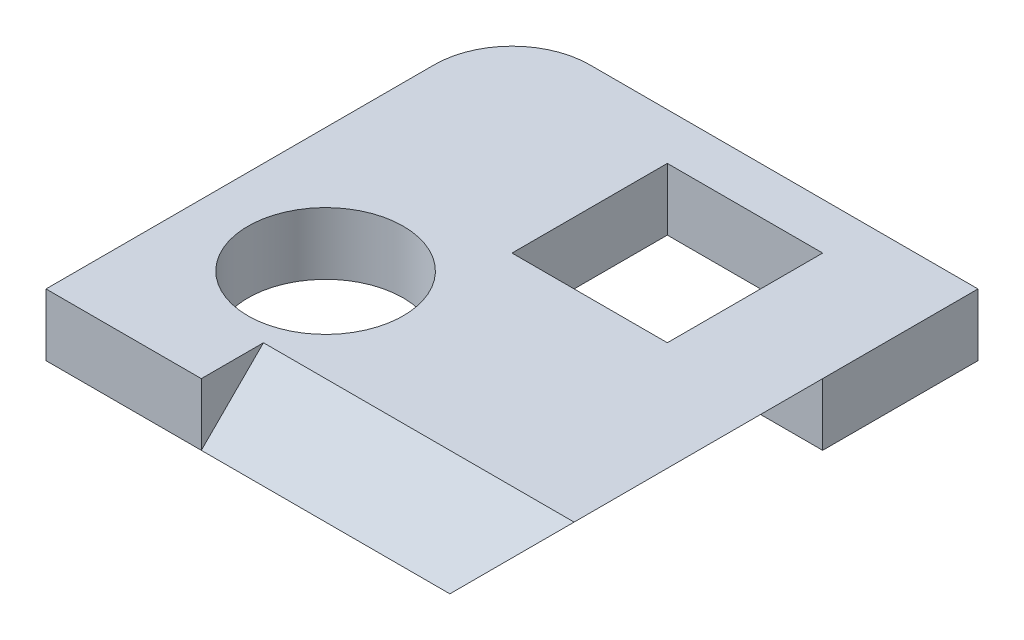
SolidWorks part; units mm, degrees
ref_plane "Ebene vorne" through (0, 0, 0) normal (0, 0, 1) x (1, 0, 0)
ref_plane "Ebene oben" through (0, 0, 0) normal (0, 1, 0) x (1, 0, 0)
ref_plane "Ebene rechts" through (0, 0, 0) normal (1, 0, 0) x (0, 0, -1)
sketch "Sketch1" plane through (0, 0, 0) normal (0, 1, 0) x (1, 0, 0)
  line L1 (0, 0) -> (30, 0)
  line L2 (0, 0) -> (0, 30)
  line L3 (0, 30) -> (30, 30)
  line L4 (30, 0) -> (30, 30)
  dimension "D1" = 30
extrude "Boss-Extrude1" add sketch "Sketch1" along normal blind 4
sketch "Sketch2" plane through (0, 4, 0) normal (0, 1, 0) x (1, 0, 0)
  line L0 (30, 30) -> (0, 30) construction
  line L1 (13, 27) -> (23, 27)
  line L2 (13, 27) -> (13, 17)
  line L3 (13, 17) -> (23, 17)
  line L4 (23, 27) -> (23, 17)
  line L5 (30, 0) -> (30, 30) construction
  line L6 (0, 30) -> (0, 0) construction
  line L7 (0, 0) -> (30, 0) construction
  circle A0 centre (8, 10) radius 5
  dimension "D4" = 10
  dimension "D1" = 3
  dimension "D2" = 7
  dimension "D3" = 10
  dimension "D5" = 8
  dimension "D6" = 10
extrude "Cut-Extrude1" cut sketch "Sketch2" against normal through all
fillet "Fillet1" radius 5 1 edges at (0, 2, -30)
sketch "Sketch3" plane through (30, 0, 0) normal (1, 0, 0) x (0, 0, -1)
  line L0 (0, 0) -> (4, 4)
  line L1 (0, 4) -> (30, 4) construction
  line L2 (4, 4) -> (0, 4)
  line L3 (0, 4) -> (0, 0)
  line L4 (0, 0) -> (30, 0) construction
  dimension "D1" = 45
extrude "Cut-Extrude2" cut sketch "Sketch3" against normal blind 20
sketch "Sketch4" plane through (0, 0, 0) normal (0, 0, 1) x (1, 0, 0)
  line L0 (30, 4) -> (26, 0)
  line L1 (10, 0) -> (30, 0) construction
  line L2 (26, 0) -> (30, 0)
  line L3 (30, 0) -> (30, 4)
  line L4 (10, 4) -> (30, 4) construction
  dimension "D1" = 45
extrude "Cut-Extrude3" cut sketch "Sketch4" against normal blind 20
